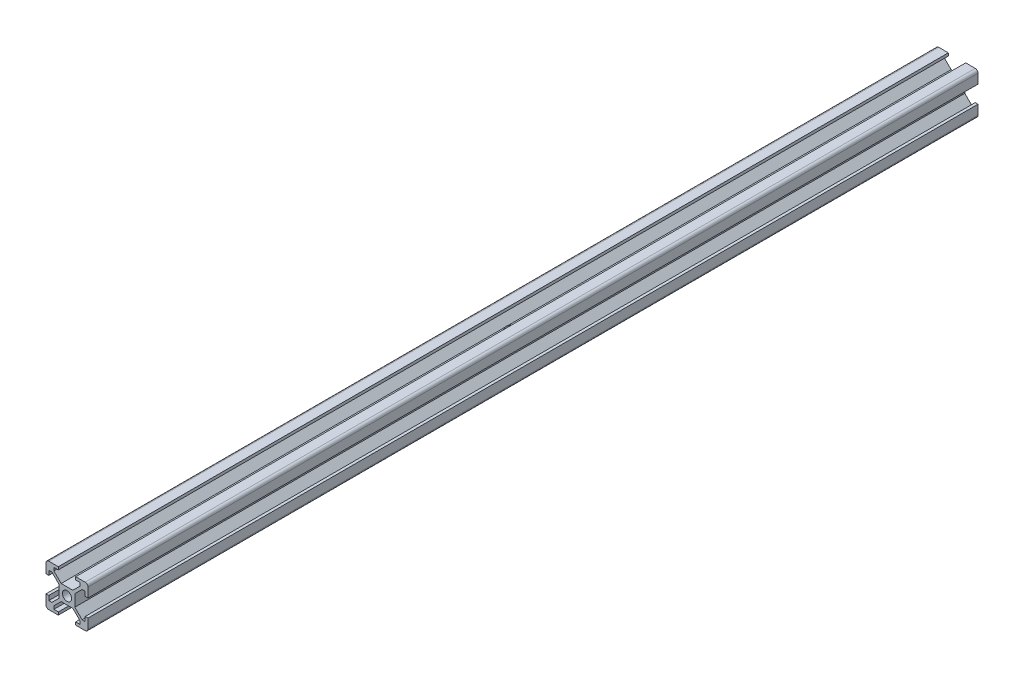
SolidWorks part; units mm, degrees
ref_plane "前视基准面" through (0, 0, 0) normal (0, 0, 1) x (1, 0, 0)
ref_plane "上视基准面" through (0, 0, 0) normal (0, 1, 0) x (1, 0, 0)
ref_plane "右视基准面" through (0, 0, 0) normal (1, 0, 0) x (0, 0, -1)
sketch "草图1" plane through (0, 0, 0) normal (0, 0, 1) x (1, 0, 0)
  line L0 (-13.1606, 0) -> (11.1587, 0) construction
  line L1 (0, 10.9428) -> (0, -12.3014) construction
  line L2 (-13.1302, 13.1302) -> (13.1302, -13.1302) construction
  line L3 (-2.0929, 2.8) -> (2.0929, 2.8)
  line L4 (-2.8, 2.0929) -> (-2.8, -2.0929)
  line L5 (-2.0929, -2.8) -> (2.0929, -2.8)
  line L6 (2.8, 2.0929) -> (2.8, -2.0929)
  line L7 (-2.0929, 2.8) -> (-4.7, 5.4071)
  line L8 (-2.8, 2.0929) -> (-5.4071, 4.7)
  line L9 (-7.5, 6.5) -> (-7.5, 3.1)
  line L10 (-7.5, 3.1) -> (-6.5, 3.1)
  line L11 (-6.5, 3.1) -> (-6.5, 4.7)
  line L12 (-6.5, 4.7) -> (-5.4071, 4.7)
  line L13 (-4.7, 6.5) -> (-4.7, 5.4071)
  line L14 (-3.1, 6.5) -> (-4.7, 6.5)
  line L15 (-3.1, 7.5) -> (-3.1, 6.5)
  line L16 (-6.5, 7.5) -> (-3.1, 7.5)
  line L17 (2.8, 2.0929) -> (5.4071, 4.7)
  line L18 (2.0929, 2.8) -> (4.7, 5.4071)
  line L19 (6.5, 7.5) -> (3.1, 7.5)
  line L20 (3.1, 7.5) -> (3.1, 6.5)
  line L21 (3.1, 6.5) -> (4.7, 6.5)
  line L22 (4.7, 6.5) -> (4.7, 5.4071)
  line L23 (6.5, 4.7) -> (5.4071, 4.7)
  line L24 (6.5, 3.1) -> (6.5, 4.7)
  line L25 (7.5, 3.1) -> (6.5, 3.1)
  line L26 (7.5, 6.5) -> (7.5, 3.1)
  line L27 (2.0929, -2.8) -> (4.7, -5.4071)
  line L28 (2.8, -2.0929) -> (5.4071, -4.7)
  line L29 (7.5, -6.5) -> (7.5, -3.1)
  line L30 (7.5, -3.1) -> (6.5, -3.1)
  line L31 (6.5, -3.1) -> (6.5, -4.7)
  line L32 (6.5, -4.7) -> (5.4071, -4.7)
  line L33 (4.7, -6.5) -> (4.7, -5.4071)
  line L34 (3.1, -6.5) -> (4.7, -6.5)
  line L35 (3.1, -7.5) -> (3.1, -6.5)
  line L36 (6.5, -7.5) -> (3.1, -7.5)
  line L37 (-2.8, -2.0929) -> (-5.4071, -4.7)
  line L38 (-2.0929, -2.8) -> (-4.7, -5.4071)
  line L39 (-6.5, -7.5) -> (-3.1, -7.5)
  line L40 (-3.1, -7.5) -> (-3.1, -6.5)
  line L41 (-3.1, -6.5) -> (-4.7, -6.5)
  line L42 (-4.7, -6.5) -> (-4.7, -5.4071)
  line L43 (-6.5, -4.7) -> (-5.4071, -4.7)
  line L44 (-6.5, -3.1) -> (-6.5, -4.7)
  line L45 (-7.5, -3.1) -> (-6.5, -3.1)
  line L46 (-7.5, -6.5) -> (-7.5, -3.1)
  circle A0 centre (0, 0) radius 1.65
  arc A1 (-7.5, 6.5) -> (-6.5, 7.5) centre (-6.5, 6.5) cw
  arc A2 (6.5, 7.5) -> (7.5, 6.5) centre (6.5, 6.5) cw
  arc A3 (7.5, -6.5) -> (6.5, -7.5) centre (6.5, -6.5) cw
  arc A4 (-6.5, -7.5) -> (-7.5, -6.5) centre (-6.5, -6.5) cw
  point P26 (-7.5, 7.5)
  point P68 (0, 0)
  dimension "D1" = 3.3
  dimension "D10" = 1
  dimension "D2" = 45
  dimension "D4" = 1
  dimension "D5" = 7.5
  dimension "D6" = 4.7
  dimension "D7" = 1
  dimension "D8" = 3.1
  dimension "D9" = 4.7
  dimension "D11" = 4
extrude "凸台-拉伸1" add sketch "草图1" along normal blind 318
cosmetic thread "装饰螺纹线1" parameters "D1"=20, "D2"=4
cosmetic thread "装饰螺纹线2" parameters "D1"=20, "D2"=4
sketch "草图12" plane through (0, 0, 0) normal (0, 1, 0) x (1, 0, 0)
  line L0 (0, 40.8179) -> (0, -346.985) construction
  line L1 (-57.9104, -159) -> (74.0068, -159) construction
  line L2 (-3.1, 0) -> (-6.5, 0) construction
  line L3 (-3.1, -318) -> (-6.5, -318) construction
  circle A0 centre (0, -159) radius 2.15
  dimension "D1" = 4.3
extrude "切除-拉伸3" cut sketch "草图12" against normal mid plane 50
